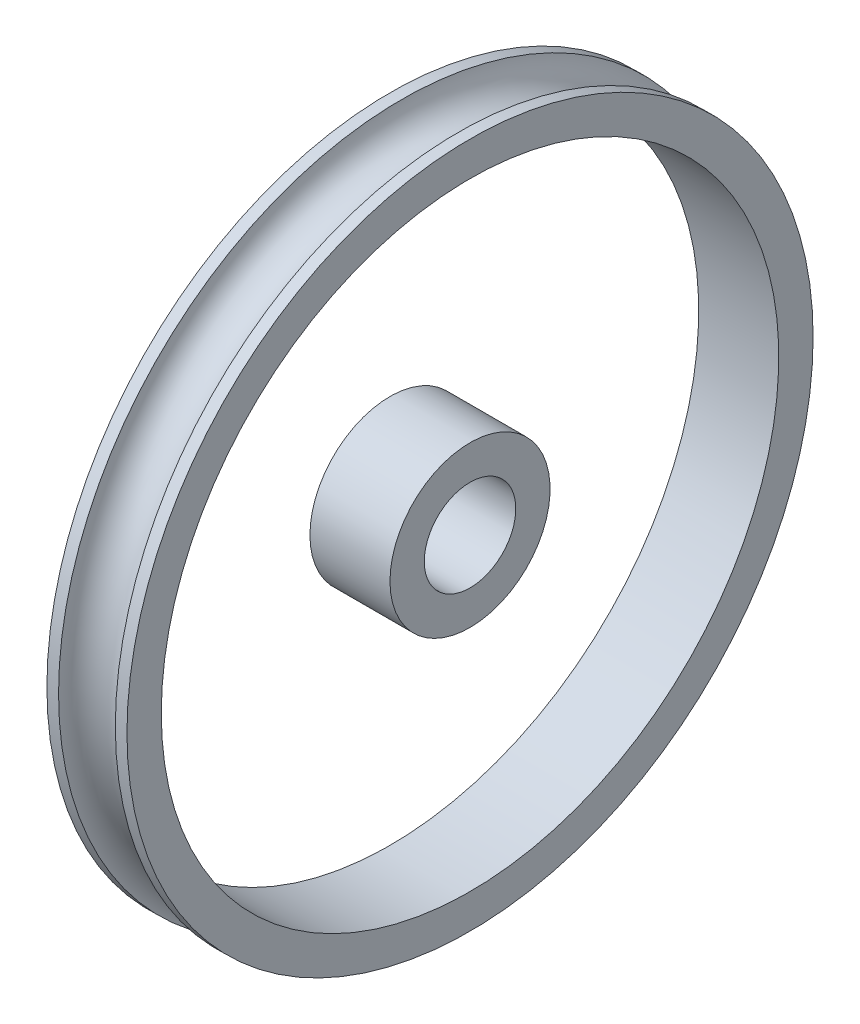
SolidWorks part; units mm, degrees
ref_plane "Front Plane" through (0, 0, 0) normal (0, 0, 1) x (1, 0, 0)
ref_plane "Top Plane" through (0, 0, 0) normal (0, 1, 0) x (1, 0, 0)
ref_plane "Right Plane" through (0, 0, 0) normal (1, 0, 0) x (0, 0, -1)
sketch "Sketch1" plane through (0, 0, 0) normal (0, 1, 0) x (1, 0, 0)
  line L0 (0, 4) -> (7, 4)
  line L1 (0, 0) -> (7, 0) construction
  line L2 (0, 4) -> (0, 7)
  line L3 (0, 30) -> (1.0181, 30)
  line L4 (7, 4) -> (7, 7)
  line L5 (0, 27) -> (7, 27)
  line L6 (0, 7) -> (7, 7)
  line L7 (5.9819, 30) -> (7, 30)
  line L8 (7, 27) -> (7, 30)
  line L9 (0, 27) -> (0, 30)
  arc A0 (1.0181, 30) -> (5.9819, 30) centre (3.5, 30.3) ccw
  dimension "D5" = 5
  dimension "D1" = 30
  dimension "D2" = 7
  dimension "D3" = 4
  dimension "D4" = 3
  dimension "D6" = 0.3
  dimension "D7" = 3
revolve "Revolve1" add sketch "Sketch1" angle 360 about L1
